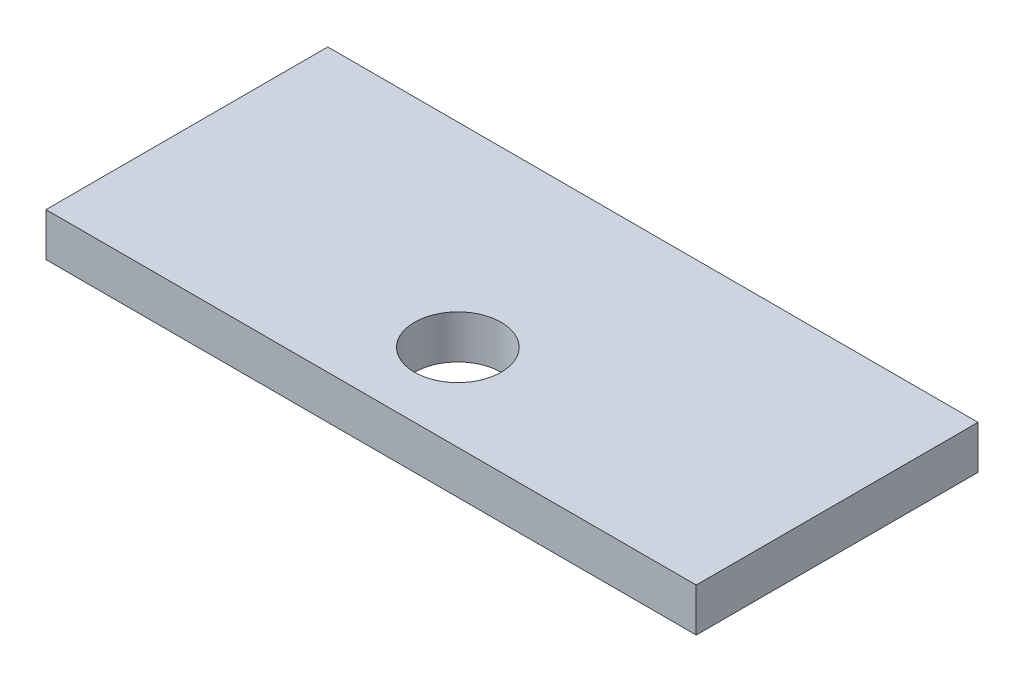
SolidWorks part; units mm, degrees
ref_plane "Front Plane" through (0, 0, 0) normal (0, 0, 1) x (1, 0, 0)
ref_plane "Top Plane" through (0, 0, 0) normal (0, 1, 0) x (1, 0, 0)
ref_plane "Right Plane" through (0, 0, 0) normal (1, 0, 0) x (0, 0, -1)
sketch "Sketch1" plane through (0, 0, 0) normal (0, 1, 0) x (1, 0, 0)
  line L1 (-75, -32.5) -> (75, -32.5)
  line L2 (-75, -32.5) -> (-75, 32.5)
  line L3 (-75, 32.5) -> (75, 32.5)
  line L4 (75, -32.5) -> (75, 32.5)
  line L5 (-75, -32.5) -> (75, 32.5) construction
  line L6 (-75, 32.5) -> (75, -32.5) construction
  point P0 (0, 0)
  dimension "D1" = 150
  dimension "D2" = 65
extrude "Boss-Extrude1" add sketch "Sketch1" along normal blind 10
sketch "Sketch2" plane through (0, 0, 0) normal (0, 1, 0) x (1, 0, 0)
  line L0 (0, 0) -> (0, -46.7949) construction
  line L1 (-75, -32.5) -> (75, -32.5) construction
  circle A0 centre (0, -12.5) radius 10
  dimension "D1" = 20
  dimension "D2" = 20
extrude "Cut-Extrude2" cut sketch "Sketch2" against normal through all and the other way through all
